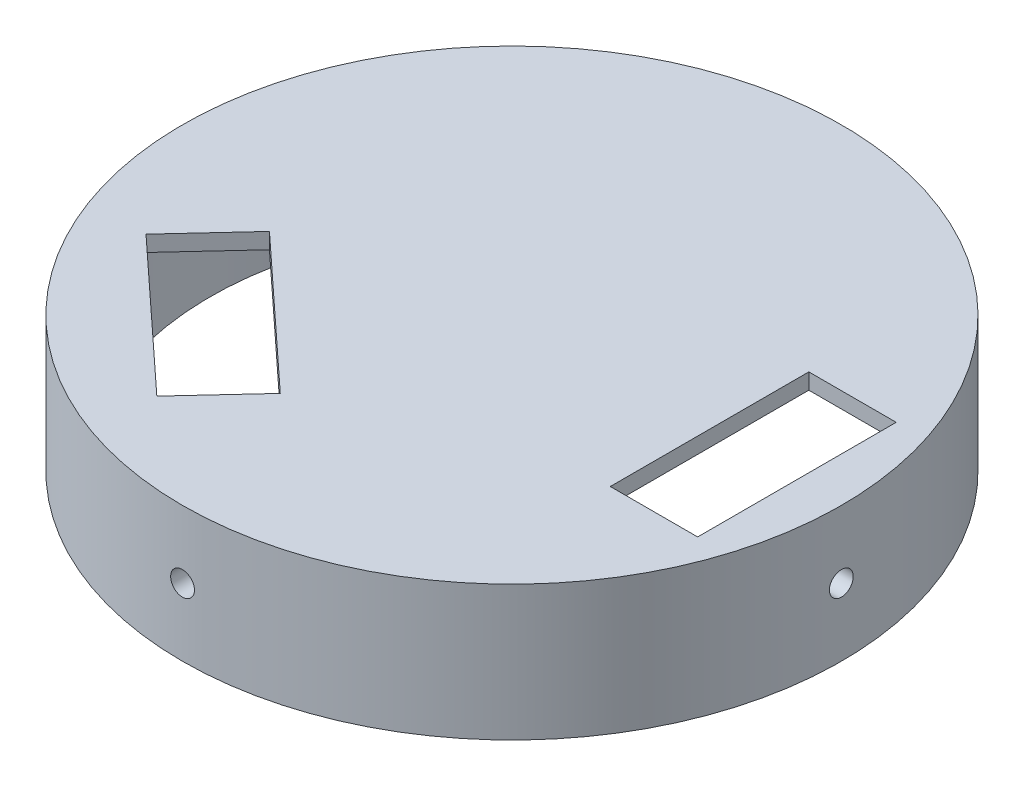
SolidWorks part; units mm, degrees
ref_plane "Front Plane" through (0, 0, 0) normal (0, 0, 1) x (1, 0, 0)
ref_plane "Top Plane" through (0, 0, 0) normal (0, 1, 0) x (1, 0, 0)
ref_plane "Right Plane" through (0, 0, 0) normal (1, 0, 0) x (0, 0, -1)
sketch "Sketch1" plane through (0, 0, 0) normal (0, 1, 0) x (1, 0, 0)
  circle A0 centre (0, 0) radius 41.5
  circle A1 centre (0, 0) radius 38
  dimension "D1" = 83
  dimension "D2" = 3.5
extrude "Boss-Extrude1" add sketch "Sketch1" along normal blind 15
sketch "Sketch2" plane through (0, 15, 0) normal (0, 1, 0) x (1, 0, 0)
  circle A0 centre (0, 0) radius 41.5
  dimension "D1" = 83
extrude "Boss-Extrude2" add sketch "Sketch2" along normal blind 2 contours A0
sketch "Sketch3" plane through (0, 17, 0) normal (0, 1, 0) x (1, 0, 0)
  line L0 (0, 0) -> (41.5, 0) construction
  line L5 (-6.0467, -23.1243) -> (-13.519, -31.1967)
  line L6 (24.8852, -12.5) -> (35.8852, -12.5)
  line L7 (24.8852, -12.5) -> (24.8852, 12.5)
  line L8 (24.8852, 12.5) -> (35.8852, 12.5)
  line L9 (35.8852, -12.5) -> (35.8852, 12.5)
  line L10 (24.8852, -12.5) -> (35.8852, 12.5) construction
  line L11 (24.8852, 12.5) -> (35.8852, -12.5) construction
  line L12 (-24.3931, -6.1417) -> (-6.0467, -23.1243)
  line L13 (-31.8654, -14.2141) -> (-13.519, -31.1967)
  line L14 (-24.3931, -6.1417) -> (-31.8654, -14.2141)
  circle A0 centre (0, 0) radius 41.5 construction
  circle A1 centre (0, 0) radius 38 construction
  point P0 (30.3852, 0)
  point P17 (1.6354, 1.4465)
  dimension "D1" = 11
  dimension "D2" = 25
  dimension "D3" = 2
extrude "Cut-Extrude1" cut sketch "Sketch3" against normal blind 3
sketch "Sketch4" plane through (0, 0, 0) normal (0, 0, 1) x (1, 0, 0)
  line L0 (0, 17) -> (0, 0) construction
  line L1 (41.5, 17) -> (-41.5, 17) construction
  circle A1 centre (0, 8.5) radius 1.5
  dimension "D1" = 3
extrude "Cut-Extrude2" cut sketch "Sketch4" against normal blind 80 and the other way blind 80
sketch "Sketch5" plane through (0, 0, 0) normal (1, 0, 0) x (0, 0, -1)
  line L0 (0, 0) -> (0, 17) construction
  line L1 (-12.5, 17) -> (12.5, 17) construction
  circle A0 centre (0, 8.5) radius 1.5
  dimension "D1" = 3
extrude "Cut-Extrude4" cut sketch "Sketch5" against normal blind 80 and the other way blind 80 contours A0
